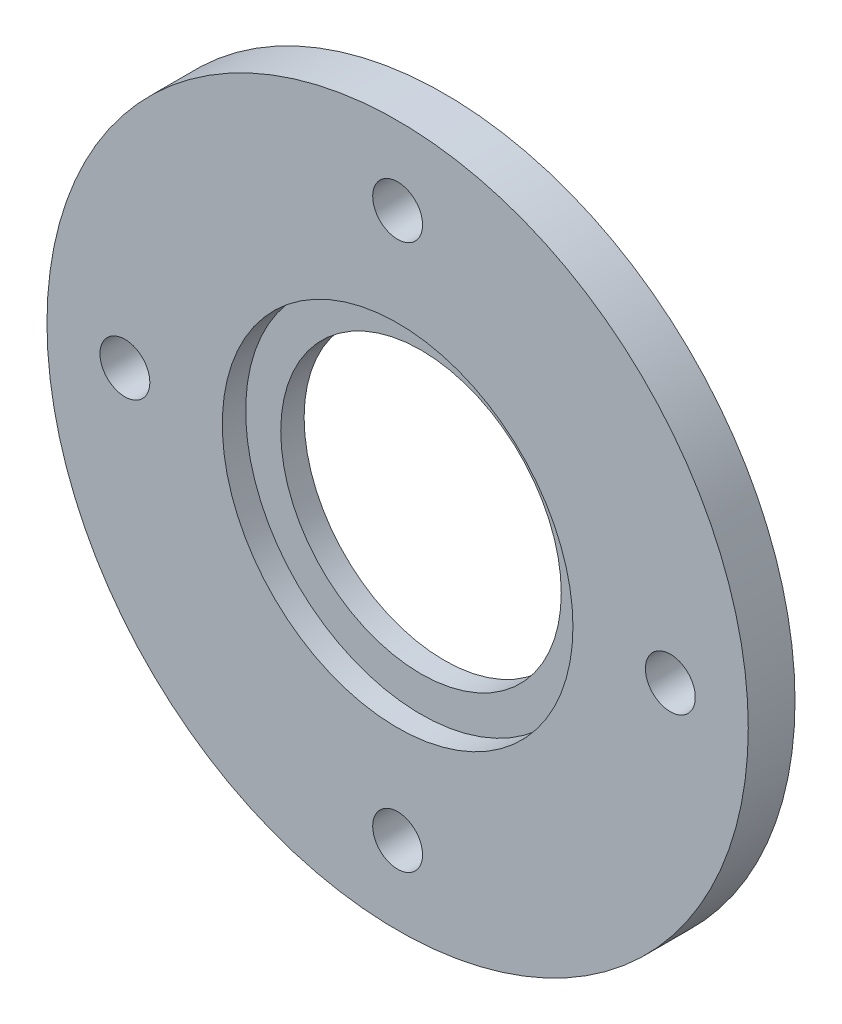
SolidWorks part; units mm, degrees
material "3.1325 (EN-AW 2017A)"
ref_plane "正面" through (0, 0, 0) normal (0, 0, 1) x (1, 0, 0)
ref_plane "平面" through (0, 0, 0) normal (0, 1, 0) x (1, 0, 0)
ref_plane "右側面" through (0, 0, 0) normal (1, 0, 0) x (0, 0, -1)
sketch "ｽｹｯﾁ1" plane through (0, 0, 0) normal (0, 0, 1) x (1, 0, 0)
  line L0 (0, 0) -> (-17.5, 0) construction
  circle A0 centre (0, 0) radius 9
  circle A1 centre (-17.5, 0) radius 1.6 construction
  circle A2 centre (0, 0) radius 22.5
  dimension "D1" = 17.5
  dimension "D2" = 18
  dimension "D3" = 3.2
  dimension "D4" = 45
extrude "ﾎﾞｽ - 押し出し1" add sketch "ｽｹｯﾁ1" along normal blind 3
sketch "ｽｹｯﾁ2" plane through (0, 0, 3) normal (0, 0, 1) x (1, 0, 0)
  circle A0 centre (-17.5, 0) radius 1.6
  circle A1 centre (-17.5, 0) radius 1.6 construction
extrude "ｶｯﾄ - 押し出し1" cut sketch "ｽｹｯﾁ2" against normal through all
pattern_circular "円形ﾊﾟﾀｰﾝ2" count 4 over 360 about axis through (0, 0, 0) along (0, 0, 1) of "ｶｯﾄ - 押し出し1"
sketch "ｽｹｯﾁ3" plane through (0, 0, 3) normal (0, 0, 1) x (1, 0, 0)
  circle A0 centre (0, 0) radius 11.25
  circle A1 centre (0, 0) radius 9
  circle A2 centre (0, 0) radius 9 construction
  dimension "D1" = 22.5
extrude "ｶｯﾄ - 押し出し2" cut sketch "ｽｹｯﾁ3" against normal blind 1.5
